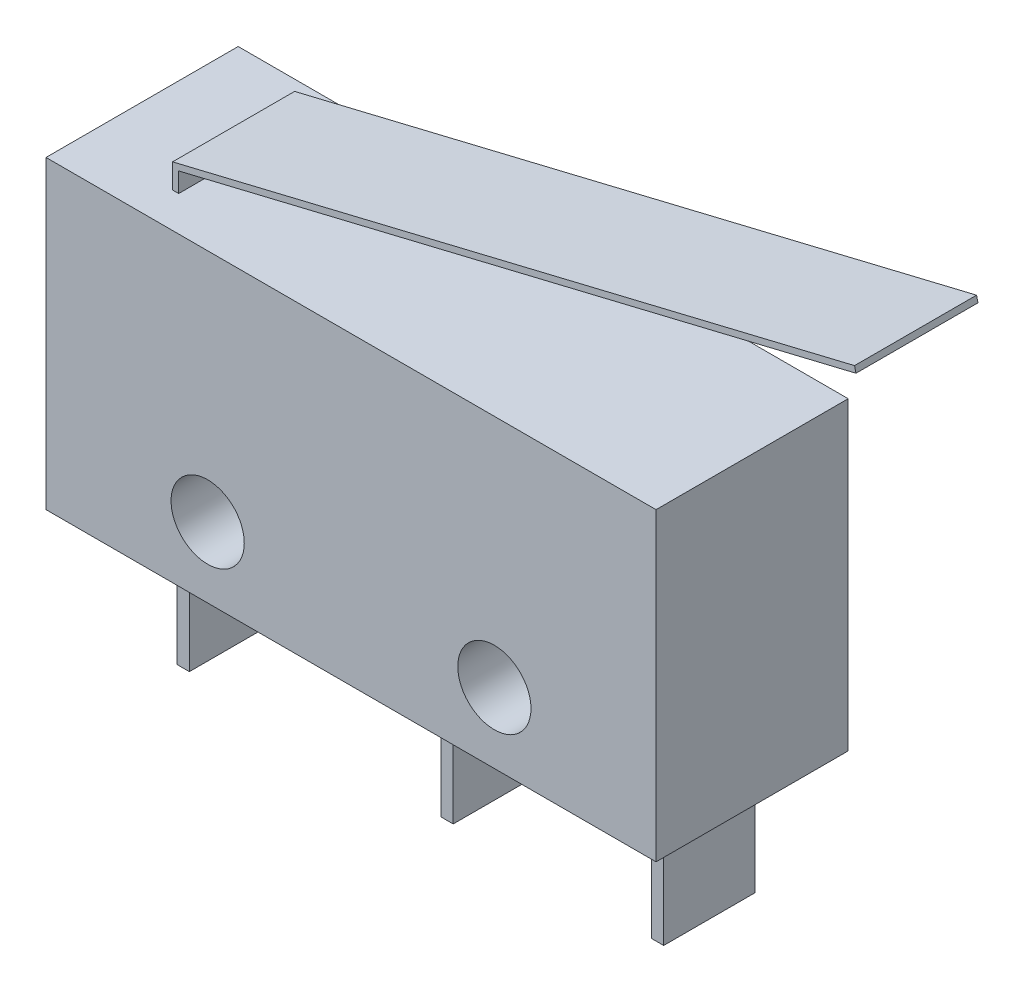
SolidWorks part; units mm, degrees
ref_plane "Plano frontal" through (0, 0, 0) normal (0, 0, 1) x (1, 0, 0)
ref_plane "Plano superior" through (0, 0, 0) normal (0, 1, 0) x (1, 0, 0)
ref_plane "Plano direito" through (0, 0, 0) normal (1, 0, 0) x (0, 0, -1)
sketch "Esboço1" plane through (0, 0, 0) normal (0, 0, 1) x (1, 0, 0)
  line L0 (1.7, -5) -> (8.2, -5)
  line L1 (-10, 5) -> (-7, 5)
  line L2 (-10, 5) -> (-10, -5)
  line L3 (-10, -5) -> (-7.35, -5)
  line L4 (10, 5) -> (10, -5)
  line L5 (-10, 5) -> (10, -5) construction
  line L6 (-10, -5) -> (10, 5) construction
  line L7 (-6.95, -5) -> (1.3, -5)
  line L8 (8.6, -5) -> (8.6, -8.9)
  line L9 (8.6, -8.9) -> (8.2, -8.9)
  line L10 (8.2, -5) -> (8.2, -8.9)
  line L11 (8.6, -5) -> (10, -5)
  line L12 (1.7, -5) -> (1.7, -8.9)
  line L13 (1.7, -8.9) -> (1.3, -8.9)
  line L14 (1.3, -5) -> (1.3, -8.9)
  line L15 (-6.8, 5.6425) -> (15.4054, 11)
  line L16 (-6.95, -5) -> (-6.95, -8.9)
  line L17 (-6.95, -8.9) -> (-7.35, -8.9)
  line L18 (-7.35, -5) -> (-7.35, -8.9)
  line L19 (15.4054, 11) -> (15.3584, 11.1944)
  line L20 (15.3584, 11.1944) -> (-7, 5.8)
  line L21 (-7, 5.8) -> (-7, 5)
  line L22 (-6.8, 5.6425) -> (-6.8, 5)
  line L23 (-6.8, 5) -> (10, 5)
  line L24 (-7, 5) -> (-6.8, 5) construction
  line L25 (0, 0) -> (0, -3.6561) construction
  circle A0 centre (-4.7, -2.7) radius 1.2
  circle A1 centre (4.7, -2.7) radius 1.2
  point P0 (0, 0)
  point P29 (3.9723, -2.3517)
  point P31 (4.6917, 3.7076)
  point P32 (3.7607, -2.3517)
  dimension "D13" = 2.4
  dimension "D14" = 7
  dimension "D15" = 6.5
  dimension "D1" = 20
  dimension "D2" = 10
  dimension "D3" = 1.4
  dimension "D4" = 6.5
  dimension "D5" = 8.25
  dimension "D6" = 0.4
  dimension "D7" = 3.9
  dimension "D8" = 3
  dimension "D9" = 0.2
  dimension "D10" = 0.8
  dimension "D11" = 23
  dimension "D12" = 6
extrude "Ressalto-extrusão1" add sketch "Esboço1" along normal blind 6.3
sketch "Esboço2" plane through (10, 0, 0) normal (1, 0, 0) x (0, 0, -1)
  line L0 (-3.15, -8.9) -> (-3.15, -5) construction
  line L1 (-6.3, -8.9) -> (0, -8.9) construction
  line L2 (0, -8.9) -> (-1.65, -8.9)
  line L3 (-6.3, -5) -> (0, -5) construction
  line L4 (0, -5) -> (0, -8.9)
  line L5 (-1.65, -5) -> (0, -5)
  line L6 (-1.65, -8.9) -> (-1.65, -5)
  line L7 (-4.65, -8.9) -> (-4.65, -5)
  line L8 (-4.65, -5) -> (-6.3, -5)
  line L9 (-6.3, -5) -> (-6.3, -8.9)
  line L10 (-6.3, -8.9) -> (-4.65, -8.9)
  point P5 (-3.15, -8.9)
  dimension "D1" = 3
extrude "Corte-extrusão1" cut sketch "Esboço2" against normal through all
sketch "Esboço3" plane through (-7, 0, 0) normal (-1, 0, 0) x (0, 0, 1)
  line L0 (1.15, 5) -> (1.15, 11.1944)
  line L1 (6.3, 5) -> (0, 5) construction
  line L2 (6.3, 11.1944) -> (0, 11.1944) construction
  line L3 (1.15, 11.1944) -> (0, 11.1944)
  line L4 (0, 11.1944) -> (0, 5)
  line L5 (0, 5) -> (1.15, 5)
  line L6 (3.15, 5) -> (3.15, 11.706) construction
  line L7 (6.3, 5) -> (5.15, 5)
  line L8 (6.3, 11.1944) -> (6.3, 5)
  line L9 (5.15, 11.1944) -> (6.3, 11.1944)
  line L10 (5.15, 5) -> (5.15, 11.1944)
  dimension "D1" = 4
extrude "Corte-extrusão2" cut sketch "Esboço3" against normal through all
